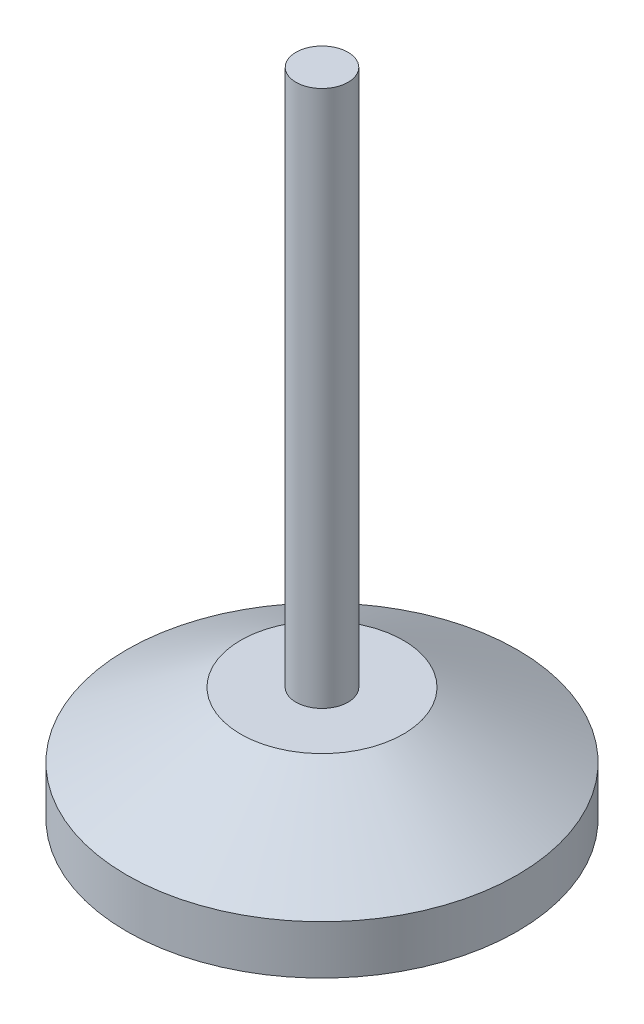
SolidWorks part; units mm, degrees
material "AISI 1035 钢 (SS)"
ref_plane "前视基准面" through (0, 0, 0) normal (0, 0, 1) x (1, 0, 0)
ref_plane "上视基准面" through (0, 0, 0) normal (0, 1, 0) x (1, 0, 0)
ref_plane "右视基准面" through (0, 0, 0) normal (1, 0, 0) x (0, 0, -1)
sketch "草图1" plane through (0, 0, 0) normal (0, 0, 1) x (1, 0, 0)
  line L0 (0, 0) -> (0, -52.2095) construction
  line L1 (0, 0) -> (-60, 0)
  line L2 (-60, 0) -> (-60, 15)
  line L3 (-60, 15) -> (-25, 35)
  line L4 (-25, 35) -> (-8, 35)
  line L5 (-8, 35) -> (-8, 200)
  line L6 (-8, 200) -> (0, 200)
  line L7 (0, 200) -> (0, 0)
  dimension "D1" = 15
  dimension "D2" = 120
  dimension "D3" = 20
  dimension "D4" = 50
  dimension "D5" = 16
  dimension "D6" = 165
revolve "旋转1" add sketch "草图1" angle 360 about L0
